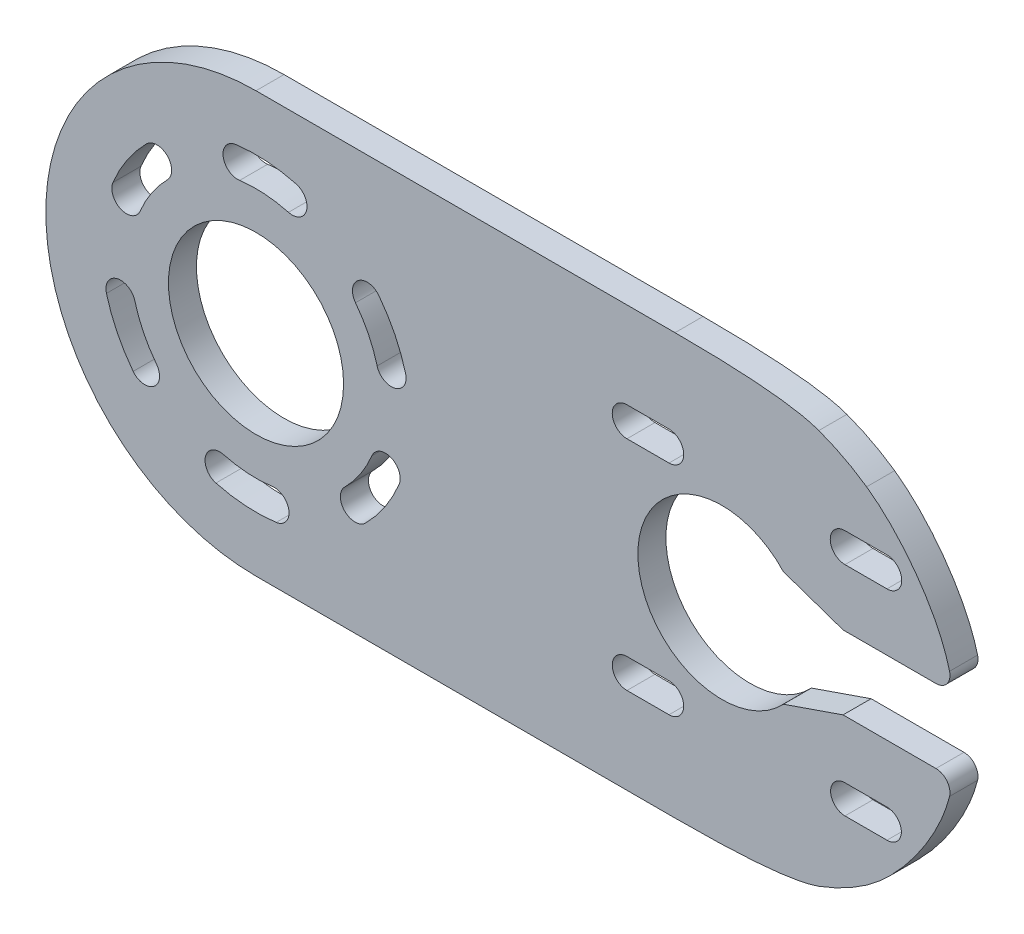
SolidWorks part; units mm, degrees
material "7075-T6 (SN)"
ref_plane "Ebene vorne" through (0, 0, 0) normal (0, 0, 1) x (1, 0, 0)
ref_plane "Ebene oben" through (0, 0, 0) normal (0, 1, 0) x (1, 0, 0)
ref_plane "Ebene rechts" through (0, 0, 0) normal (1, 0, 0) x (0, 0, -1)
sketch "Skizze1" plane through (0, 0, 0) normal (0, 0, 1) x (1, 0, 0)
  line L0 (60.6188, -25.1224) -> (53.122, -24.4665)
  line L1 (42.7599, -29.8607) -> (38.9972, -36.3779)
  line L2 (38.9972, -36.3779) -> (28.9972, -36.3779)
  line L3 (28.9972, -36.3779) -> (26.3991, -31.8779)
  line L4 (23.801, -30.3779) -> (-36.0028, -30.3779)
  line L5 (-36.0028, 29.6221) -> (23.801, 29.6221)
  line L6 (26.3991, 31.1221) -> (28.9972, 35.6221)
  line L7 (28.9972, 35.6221) -> (38.9972, 35.6221)
  line L8 (38.9972, 35.6221) -> (42.7599, 29.1049)
  line L9 (53.122, 23.7107) -> (60.6188, 24.3666)
  line L10 (60.6188, 24.3666) -> (66.3546, 16.1751)
  line L11 (66.3546, 16.1751) -> (63.1738, 9.3539)
  line L12 (61.0423, 4.8721) -> (47.7853, 4.8721)
  line L13 (47.7853, 4.8721) -> (39.265, 7.8151)
  line L14 (39.265, -8.5709) -> (47.7853, -5.6279)
  line L15 (47.7853, -5.6279) -> (61.0423, -5.6279)
  line L16 (63.1738, -10.1097) -> (66.3546, -16.9309)
  line L17 (66.3546, -16.9309) -> (60.6188, -25.1224)
  line L18 (54.0535, -13.8842) -> (48.0535, -13.8842)
  line L19 (48.0535, -17.9842) -> (54.0535, -17.9842)
  line L20 (22.9409, -13.8342) -> (16.9409, -13.8342)
  line L21 (16.9409, -18.0342) -> (22.9409, -18.0342)
  line L22 (54.0535, 17.2785) -> (48.0535, 17.2785)
  line L23 (48.0535, 13.0785) -> (54.0535, 13.0785)
  line L24 (22.9409, 17.2785) -> (16.9409, 17.2785)
  line L25 (16.9409, 13.0785) -> (22.9409, 13.0785)
  line L26 (-36.0028, -0.3779) -> (-38.6133, 19.451) construction
  line L27 (-36.0028, -0.3779) -> (-30.8264, 18.9406) construction
  line L28 (16.9409, 15.1785) -> (22.9409, 15.1785) construction
  line L29 (48.0535, -15.9342) -> (54.0535, -15.9342) construction
  line L30 (-66.0028, -0.3779) -> (65.8927, -0.3779) construction
  arc A0 (53.122, -24.4665) -> (51.1457, -24.9935) centre (52.8605, -27.4551) ccw
  arc A1 (44.3252, -28.544) -> (51.1457, -24.9935) centre (33.9972, -0.3779) ccw
  arc A2 (44.3252, -28.544) -> (42.7599, -29.8607) centre (45.358, -31.3607) ccw
  arc A3 (26.3991, -31.8779) -> (23.801, -30.3779) centre (23.801, -33.3779) ccw
  arc A4 (-36.0028, 29.6221) -> (-36.0028, -30.3779) centre (-36.0028, -0.3779) ccw
  arc A5 (23.801, 29.6221) -> (26.3991, 31.1221) centre (23.801, 32.6221) ccw
  arc A6 (42.7599, 29.1049) -> (44.3252, 27.7883) centre (45.358, 30.6049) ccw
  arc A7 (51.1457, 24.2378) -> (44.3252, 27.7883) centre (33.9972, -0.3779) ccw
  arc A8 (51.1457, 24.2378) -> (53.122, 23.7107) centre (52.8605, 26.6993) ccw
  arc A9 (63.1738, 9.3539) -> (62.9825, 7.3577) centre (65.8927, 8.086) ccw
  arc A10 (61.0423, 4.8721) -> (62.9825, 7.3577) centre (61.0423, 6.8721) ccw
  arc A11 (39.265, 7.8151) -> (39.265, -8.5709) centre (30.4972, -0.3779) ccw
  arc A12 (62.9825, -8.1135) -> (61.0423, -5.6279) centre (61.0423, -7.6279) ccw
  arc A13 (62.9825, -8.1135) -> (63.1738, -10.1097) centre (65.8927, -8.8418) ccw
  circle A14 centre (61.0292, -19.3059) radius 1.6
  circle A15 centre (33.9972, -33.3779) radius 1.6
  arc A16 (48.0535, -13.8842) -> (48.0535, -17.9842) centre (48.0535, -15.9342) ccw
  arc A17 (54.0535, -17.9842) -> (54.0535, -13.8842) centre (54.0535, -15.9342) ccw
  arc A18 (16.9409, -13.8342) -> (16.9409, -18.0342) centre (16.9409, -15.9342) ccw
  arc A19 (22.9409, -18.0342) -> (22.9409, -13.8342) centre (22.9409, -15.9342) ccw
  arc A20 (-40.6357, -17.668) -> (-33.6664, -18.1248) centre (-36.0028, -0.3779) ccw
  arc A21 (-40.6357, -17.668) -> (-41.7227, -21.7248) centre (-41.1792, -19.6964) ccw
  arc A22 (-41.7227, -21.7248) -> (-33.1182, -22.2888) centre (-36.0028, -0.3779) ccw
  arc A23 (-33.1182, -22.2888) -> (-33.6664, -18.1248) centre (-33.3923, -20.2068) ccw
  arc A24 (-20.3757, -16.0049) -> (-15.5851, -8.8352) centre (-36.0028, -0.3779) ccw
  arc A25 (-15.5851, -8.8352) -> (-19.4654, -7.2279) centre (-17.5252, -8.0316) ccw
  arc A26 (-23.3456, -13.0351) -> (-19.4654, -7.2279) centre (-36.0028, -0.3779) ccw
  arc A27 (-23.3456, -13.0351) -> (-20.3757, -16.0049) centre (-21.8607, -14.52) ccw
  arc A28 (-53.5359, -13.8315) -> (-50.2038, -11.2747) centre (-51.8699, -12.5531) ccw
  arc A29 (-53.2929, -5.0107) -> (-50.2038, -11.2747) centre (-36.0028, -0.3779) ccw
  arc A30 (-53.2929, -5.0107) -> (-57.3498, -6.0978) centre (-55.3213, -5.5543) ccw
  arc A31 (-57.3498, -6.0978) -> (-53.5359, -13.8315) centre (-36.0028, -0.3779) ccw
  circle A32 centre (-36.0028, -0.3779) radius 12.5
  circle A33 centre (61.0292, 18.5501) radius 1.6
  circle A34 centre (33.9972, 32.6221) radius 1.6
  arc A35 (-14.6558, 5.342) -> (-18.4697, 13.0757) centre (-36.0028, -0.3779) ccw
  arc A36 (-18.4697, 13.0757) -> (-21.8018, 10.5189) centre (-20.1357, 11.7973) ccw
  arc A37 (-18.7127, 4.255) -> (-21.8018, 10.5189) centre (-36.0028, -0.3779) ccw
  arc A38 (-18.7127, 4.255) -> (-14.6558, 5.342) centre (-16.6843, 4.7985) ccw
  arc A39 (48.0535, 17.2785) -> (48.0535, 13.0785) centre (48.0535, 15.1785) ccw
  arc A40 (54.0535, 13.0785) -> (54.0535, 17.2785) centre (54.0535, 15.1785) ccw
  arc A41 (16.9409, 17.2785) -> (16.9409, 13.0785) centre (16.9409, 15.1785) ccw
  arc A42 (22.9409, 13.0785) -> (22.9409, 17.2785) centre (22.9409, 15.1785) ccw
  arc A43 (-48.66, 12.2793) -> (-52.5402, 6.4721) centre (-36.0028, -0.3779) ccw
  arc A44 (-48.66, 12.2793) -> (-51.6299, 15.2492) centre (-50.1449, 13.7642) ccw
  arc A45 (-51.6299, 15.2492) -> (-56.4205, 8.0794) centre (-36.0028, -0.3779) ccw
  arc A46 (-56.4205, 8.0794) -> (-52.5402, 6.4721) centre (-54.4804, 7.2758) ccw
  arc A47 (-38.8874, 21.533) -> (-38.3392, 17.369) centre (-38.6133, 19.451) ccw
  arc A48 (-31.3699, 16.9122) -> (-38.3392, 17.369) centre (-36.0028, -0.3779) ccw
  arc A49 (-31.3699, 16.9122) -> (-30.2829, 20.9691) centre (-30.8264, 18.9406) ccw
  arc A50 (-30.2829, 20.9691) -> (-38.8874, 21.533) centre (-36.0028, -0.3779) ccw
  circle A51 centre (-36.0028, -0.3779) radius 20 construction
  dimension "D1" = 40
  dimension "D3" = 30
  dimension "D2" = 22.5
extrude "Aufsatz-Linear austragen1" [suppressed] add sketch "Skizze1" along normal blind 4
sketch "Skizze2" plane through (0, 0, 0) normal (0, 0, 1) x (1, 0, 0)
  line L2 (23.801, 29.6221) -> (39.324, 29.6221) construction
  line L6 (39.324, 29.6221) -> (44.3252, 27.7883) construction
  line L7 (-66.0028, -0.3779) -> (65.8927, -0.3779) construction
  line L8 (16.9409, 15.1785) -> (22.9409, 15.1785) construction
  line L9 (48.0535, -15.9342) -> (54.0535, -15.9342) construction
  line L10 (51.1457, 24.2378) -> (55.926, 20.9075) construction
  line L12 (61.3703, 13.7991) -> (62.9825, 7.3577) construction
  line L16 (-36.0028, 29.6221) -> (23.801, 29.6221) construction
  line L17 (55.926, 20.9075) -> (61.3703, 13.7991) construction
  line L18 (58.6482, 17.3533) -> (35.4972, -0.3779) construction
  line L19 (22.9409, 17.2785) -> (16.9409, 17.2785) construction
  line L20 (16.9409, 13.0785) -> (22.9409, 13.0785) construction
  line L21 (48.0535, 13.0785) -> (54.0535, 13.0785) construction
  line L22 (54.0535, 17.2785) -> (48.0535, 17.2785) construction
  line L23 (48.0535, -17.9842) -> (54.0535, -17.9842) construction
  line L24 (54.0535, -13.8842) -> (48.0535, -13.8842) construction
  line L25 (22.9409, -13.8342) -> (16.9409, -13.8342) construction
  line L26 (16.9409, -18.0342) -> (22.9409, -18.0342) construction
  line L27 (23.801, -30.3779) -> (-36.0028, -30.3779) construction
  line L28 (47.7853, -5.6279) -> (61.0423, -5.6279) construction
  line L29 (39.265, -8.5709) -> (47.7853, -5.6279) construction
  line L30 (47.7853, 4.8721) -> (39.265, 7.8151) construction
  line L31 (61.0423, 4.8721) -> (47.7853, 4.8721) construction
  line L32 (-36.0028, 29.6221) -> (23.801, 29.6221)
  line L33 (22.9409, 17.2785) -> (16.9409, 17.2785)
  line L34 (16.9409, 13.0785) -> (22.9409, 13.0785)
  line L35 (48.0535, 13.0785) -> (54.0535, 13.0785)
  line L36 (54.0535, 17.2785) -> (48.0535, 17.2785)
  line L37 (48.0535, -17.9842) -> (54.0535, -17.9842)
  line L38 (54.0535, -13.8842) -> (48.0535, -13.8842)
  line L39 (22.9409, -13.8342) -> (16.9409, -13.8342)
  line L40 (16.9409, -18.0342) -> (22.9409, -18.0342)
  line L41 (23.801, -30.3779) -> (-36.0028, -30.3779)
  line L42 (47.7853, -5.6279) -> (61.0423, -5.6279)
  line L43 (39.265, -8.5709) -> (47.7853, -5.6279)
  line L44 (47.7853, 4.8721) -> (39.265, 7.8151)
  line L45 (61.0423, 4.8721) -> (47.7853, 4.8721)
  line L46 (-66.0028, -0.3779) -> (65.8927, -0.3779) construction
  line L47 (51.1457, -24.9935) -> (55.926, -21.6633) construction
  line L48 (55.926, -21.6633) -> (61.3703, -14.5549) construction
  line L49 (61.3703, -14.5549) -> (62.9825, -8.1135) construction
  line L50 (23.801, -30.3779) -> (39.324, -30.3779) construction
  line L51 (39.324, -30.3779) -> (44.3252, -28.544) construction
  circle A10 centre (35.4972, -0.3779) radius 22 construction
  arc A15 (23.801, 29.6221) -> (26.3991, 31.1221) centre (23.801, 32.6221) ccw construction
  arc A19 (51.1457, 24.2378) -> (44.3252, 27.7883) centre (33.9972, -0.3779) ccw construction
  arc A20 (61.0423, 4.8721) -> (62.9825, 7.3577) centre (61.0423, 6.8721) ccw construction
  arc A21 (-23.3456, -13.0351) -> (-19.4654, -7.2279) centre (-36.0028, -0.3779) ccw construction
  arc A22 (-15.5851, -8.8352) -> (-19.4654, -7.2279) centre (-17.5252, -8.0316) ccw construction
  arc A23 (-20.3757, -16.0049) -> (-15.5851, -8.8352) centre (-36.0028, -0.3779) ccw construction
  arc A24 (-23.3456, -13.0351) -> (-20.3757, -16.0049) centre (-21.8607, -14.52) ccw construction
  arc A25 (-40.6357, -17.668) -> (-33.6664, -18.1248) centre (-36.0028, -0.3779) ccw construction
  arc A26 (-33.1182, -22.2888) -> (-33.6664, -18.1248) centre (-33.3923, -20.2068) ccw construction
  arc A27 (-41.7227, -21.7248) -> (-33.1182, -22.2888) centre (-36.0028, -0.3779) ccw construction
  arc A28 (-40.6357, -17.668) -> (-41.7227, -21.7248) centre (-41.1792, -19.6964) ccw construction
  circle A29 centre (-36.0028, -0.3779) radius 12.5 construction
  arc A30 (-53.2929, -5.0107) -> (-50.2038, -11.2747) centre (-36.0028, -0.3779) ccw construction
  arc A31 (-53.5359, -13.8315) -> (-50.2038, -11.2747) centre (-51.8699, -12.5531) ccw construction
  arc A32 (-57.3498, -6.0978) -> (-53.5359, -13.8315) centre (-36.0028, -0.3779) ccw construction
  arc A33 (-53.2929, -5.0107) -> (-57.3498, -6.0978) centre (-55.3213, -5.5543) ccw construction
  arc A34 (-48.66, 12.2793) -> (-52.5402, 6.4721) centre (-36.0028, -0.3779) ccw construction
  arc A35 (-56.4205, 8.0794) -> (-52.5402, 6.4721) centre (-54.4804, 7.2758) ccw construction
  arc A36 (-51.6299, 15.2492) -> (-56.4205, 8.0794) centre (-36.0028, -0.3779) ccw construction
  arc A37 (-48.66, 12.2793) -> (-51.6299, 15.2492) centre (-50.1449, 13.7642) ccw construction
  arc A38 (-31.3699, 16.9122) -> (-38.3392, 17.369) centre (-36.0028, -0.3779) ccw construction
  arc A39 (-38.8874, 21.533) -> (-38.3392, 17.369) centre (-38.6133, 19.451) ccw construction
  arc A40 (-30.2829, 20.9691) -> (-38.8874, 21.533) centre (-36.0028, -0.3779) ccw construction
  arc A41 (-31.3699, 16.9122) -> (-30.2829, 20.9691) centre (-30.8264, 18.9406) ccw construction
  arc A42 (-18.7127, 4.255) -> (-14.6558, 5.342) centre (-16.6843, 4.7985) ccw construction
  arc A43 (-18.4697, 13.0757) -> (-21.8018, 10.5189) centre (-20.1357, 11.7973) ccw construction
  arc A44 (-14.6558, 5.342) -> (-18.4697, 13.0757) centre (-36.0028, -0.3779) ccw construction
  arc A45 (-18.7127, 4.255) -> (-21.8018, 10.5189) centre (-36.0028, -0.3779) ccw construction
  arc A46 (-36.0028, 29.6221) -> (-36.0028, -30.3779) centre (-36.0028, -0.3779) ccw construction
  arc A47 (16.9409, 17.2785) -> (16.9409, 13.0785) centre (16.9409, 15.1785) ccw construction
  arc A48 (22.9409, 13.0785) -> (22.9409, 17.2785) centre (22.9409, 15.1785) ccw construction
  arc A49 (48.0535, 17.2785) -> (48.0535, 13.0785) centre (48.0535, 15.1785) ccw construction
  arc A50 (54.0535, 13.0785) -> (54.0535, 17.2785) centre (54.0535, 15.1785) ccw construction
  arc A51 (54.0535, -17.9842) -> (54.0535, -13.8842) centre (54.0535, -15.9342) ccw construction
  arc A52 (48.0535, -13.8842) -> (48.0535, -17.9842) centre (48.0535, -15.9342) ccw construction
  arc A53 (22.9409, -18.0342) -> (22.9409, -13.8342) centre (22.9409, -15.9342) ccw construction
  arc A54 (16.9409, -13.8342) -> (16.9409, -18.0342) centre (16.9409, -15.9342) ccw construction
  arc A55 (44.3252, -28.544) -> (51.1457, -24.9935) centre (33.9972, -0.3779) ccw construction
  arc A56 (62.9825, -8.1135) -> (61.0423, -5.6279) centre (61.0423, -7.6279) ccw construction
  arc A57 (39.265, 7.8151) -> (39.265, -8.5709) centre (30.4972, -0.3779) ccw construction
  arc A58 (51.1457, 24.2378) -> (44.3252, 27.7883) centre (33.9972, -0.3779) ccw
  arc A59 (-23.3456, -13.0351) -> (-19.4654, -7.2279) centre (-36.0028, -0.3779) ccw
  arc A60 (-15.5851, -8.8352) -> (-19.4654, -7.2279) centre (-17.5252, -8.0316) ccw
  arc A61 (-20.3757, -16.0049) -> (-15.5851, -8.8352) centre (-36.0028, -0.3779) ccw
  arc A62 (-23.3456, -13.0351) -> (-20.3757, -16.0049) centre (-21.8607, -14.52) ccw
  arc A63 (-40.6357, -17.668) -> (-33.6664, -18.1248) centre (-36.0028, -0.3779) ccw
  arc A64 (-33.1182, -22.2888) -> (-33.6664, -18.1248) centre (-33.3923, -20.2068) ccw
  arc A65 (-41.7227, -21.7248) -> (-33.1182, -22.2888) centre (-36.0028, -0.3779) ccw
  arc A66 (-40.6357, -17.668) -> (-41.7227, -21.7248) centre (-41.1792, -19.6964) ccw
  circle A67 centre (-36.0028, -0.3779) radius 12.5
  arc A68 (-53.2929, -5.0107) -> (-50.2038, -11.2747) centre (-36.0028, -0.3779) ccw
  arc A69 (-53.5359, -13.8315) -> (-50.2038, -11.2747) centre (-51.8699, -12.5531) ccw
  arc A70 (-57.3498, -6.0978) -> (-53.5359, -13.8315) centre (-36.0028, -0.3779) ccw
  arc A71 (-53.2929, -5.0107) -> (-57.3498, -6.0978) centre (-55.3213, -5.5543) ccw
  arc A72 (-48.66, 12.2793) -> (-52.5402, 6.4721) centre (-36.0028, -0.3779) ccw
  arc A73 (-56.4205, 8.0794) -> (-52.5402, 6.4721) centre (-54.4804, 7.2758) ccw
  arc A74 (-51.6299, 15.2492) -> (-56.4205, 8.0794) centre (-36.0028, -0.3779) ccw
  arc A75 (-48.66, 12.2793) -> (-51.6299, 15.2492) centre (-50.1449, 13.7642) ccw
  arc A76 (-31.3699, 16.9122) -> (-38.3392, 17.369) centre (-36.0028, -0.3779) ccw
  arc A77 (-38.8874, 21.533) -> (-38.3392, 17.369) centre (-38.6133, 19.451) ccw
  arc A78 (-30.2829, 20.9691) -> (-38.8874, 21.533) centre (-36.0028, -0.3779) ccw
  arc A79 (-31.3699, 16.9122) -> (-30.2829, 20.9691) centre (-30.8264, 18.9406) ccw
  arc A80 (-18.7127, 4.255) -> (-14.6558, 5.342) centre (-16.6843, 4.7985) ccw
  arc A81 (-18.4697, 13.0757) -> (-21.8018, 10.5189) centre (-20.1357, 11.7973) ccw
  arc A82 (-14.6558, 5.342) -> (-18.4697, 13.0757) centre (-36.0028, -0.3779) ccw
  arc A83 (-18.7127, 4.255) -> (-21.8018, 10.5189) centre (-36.0028, -0.3779) ccw
  arc A84 (-36.0028, 29.6221) -> (-36.0028, -30.3779) centre (-36.0028, -0.3779) ccw
  arc A85 (16.9409, 17.2785) -> (16.9409, 13.0785) centre (16.9409, 15.1785) ccw
  arc A86 (22.9409, 13.0785) -> (22.9409, 17.2785) centre (22.9409, 15.1785) ccw
  arc A87 (48.0535, 17.2785) -> (48.0535, 13.0785) centre (48.0535, 15.1785) ccw
  arc A88 (54.0535, 13.0785) -> (54.0535, 17.2785) centre (54.0535, 15.1785) ccw
  arc A89 (54.0535, -17.9842) -> (54.0535, -13.8842) centre (54.0535, -15.9342) ccw
  arc A90 (48.0535, -13.8842) -> (48.0535, -17.9842) centre (48.0535, -15.9342) ccw
  arc A91 (22.9409, -18.0342) -> (22.9409, -13.8342) centre (22.9409, -15.9342) ccw
  arc A92 (16.9409, -13.8342) -> (16.9409, -18.0342) centre (16.9409, -15.9342) ccw
  arc A93 (44.3252, -28.544) -> (51.1457, -24.9935) centre (33.9972, -0.3779) ccw
  arc A94 (62.9825, -8.1135) -> (61.0423, -5.6279) centre (61.0423, -7.6279) ccw
  arc A95 (39.265, 7.8151) -> (39.265, -8.5709) centre (30.4972, -0.3779) ccw
  arc A96 (61.0423, 4.8721) -> (62.9825, 7.3577) centre (61.0423, 6.8721) ccw
  spline S0 degree 2 poles (23.801, 29.6221) (39.324, 29.6221) (44.3252, 27.7883) knots 0 0 0 1 1 1
  spline S1 degree 3 poles (51.1457, 24.2378) (55.926, 20.9075) (61.3703, 13.7991) (62.9825, 7.3577) knots 0 0 0 0 1 1 1 1
  spline S2 degree 3 poles (51.1457, -24.9935) (55.926, -21.6633) (61.3703, -14.5549) (62.9825, -8.1135) knots 0 0 0 0 1 1 1 1
  spline S3 degree 2 poles (23.801, -30.3779) (39.324, -30.3779) (44.3252, -28.544) knots 0 0 0 1 1 1
  point P21 (19.9409, 15.1785)
  point P30 (51.0535, -15.9342)
  point P46 (0, 0)
extrude "Aufsatz-Linear austragen2" add sketch "Skizze2" along normal blind 4 contours L41 S3 A93 S2 A94 L42 L43 A95 L44 L45 A96 S1 A58 S0 L32 A84 A80 A83 A81 A82 A62 A59 A60 A61 A66 A63 A64 A65 A67 A71 A68 A69 A70 A75 A72 A73 A74 A79 A76 A77 A78 A86 L34
